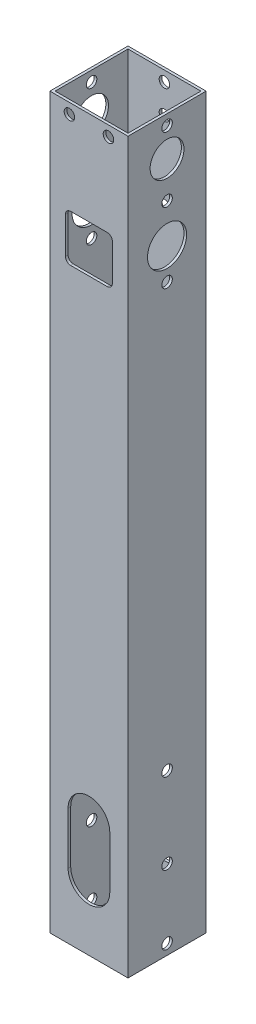
SolidWorks part; units mm, degrees
material "6063-T5"
ref_plane "前视基准面" through (0, 0, 0) normal (0, 0, 1) x (1, 0, 0)
ref_plane "上视基准面" through (0, 0, 0) normal (0, 1, 0) x (1, 0, 0)
ref_plane "右视基准面" through (0, 0, 0) normal (1, 0, 0) x (0, 0, -1)
other "Configuration Table"
sketch "草图1" plane through (0, 0, 0) normal (0, 1, 0) x (1, 0, 0)
  line L1 (-15, -15) -> (15, -15)
  line L2 (-15, -15) -> (-15, 15)
  line L3 (-15, 15) -> (15, 15)
  line L4 (15, -15) -> (15, 15)
  line L5 (-15, -15) -> (15, 15) construction
  line L6 (-15, 15) -> (15, -15) construction
  point P0 (0, 0)
  dimension "D1" = 30
extrude "凸台-拉伸1" add sketch "草图1" along normal mid plane 280
sketch "草图2" plane through (0, 0, 0) normal (0, 1, 0) x (1, 0, 0)
  line L8 (14, -14) -> (14, 14)
  line L9 (14, 14) -> (-14, 14)
  line L10 (-14, 14) -> (-14, -14)
  line L11 (-14, -14) -> (14, -14)
  line L12 (14, -14) -> (14, 14)
  line L13 (14, 14) -> (-14, 14)
  line L14 (-14, 14) -> (-14, -14)
  line L15 (-14, -14) -> (14, -14)
  dimension "D1" = 1
extrude "切除-拉伸1" cut sketch "草图2" against normal through all both and the other way through all
sketch "草图3" plane through (-15, 0, 0) normal (-1, 0, 0) x (0, 0, 1)
  circle A0 centre (0, -78.5) radius 2.025
  circle A1 centre (0, -109.5) radius 2.025
  circle A2 centre (0, -136) radius 2.025
  circle A3 centre (0, -109.5) radius 2.025 construction
  circle A4 centre (0, -78.5) radius 2.025 construction
  circle A5 centre (0, -136) radius 2.025 construction
  dimension "D1" = 4.05
extrude "切除-拉伸2" cut sketch "草图3" against normal through all both
sketch "草图5" plane through (-15, 0, 0) normal (-1, 0, 0) x (0, 0, 1)
  line L0 (15, 140) -> (15, -140) construction
  line L1 (-15, 140) -> (15, 140) construction
  circle A0 centre (0, 136) radius 2.025
  circle A1 centre (0, 111) radius 2.025
  circle A2 centre (0, 84) radius 2.025
  dimension "D1" = 4.05
  dimension "D2" = 15
  dimension "D4" = 25
  dimension "D5" = 27
  dimension "D3" = 4
extrude "切除-拉伸3" cut sketch "草图5" against normal through all
sketch "草图6" plane through (0, 0, -15) normal (0, 0, -1) x (-1, 0, 0)
  line L0 (-15, 140) -> (15, 140) construction
  line L1 (15, 140) -> (15, -140) construction
  circle A0 centre (0, 95) radius 2.025
  circle A1 centre (0, 125) radius 2.025
  dimension "D1" = 4.05
  dimension "D2" = 15
  dimension "D3" = 30
  dimension "D4" = 15
extrude "切除-拉伸4" cut sketch "草图6" against normal up to surface (1 mm away) up to face at (0, 0, -14)
sketch "草图7" plane through (0, 0, 14) normal (0, 0, -1) x (-1, 0, 0)
  line L1 (-9, 86) -> (9, 86)
  line L2 (-9, 86) -> (-9, 104)
  line L3 (-9, 104) -> (9, 104)
  line L4 (9, 86) -> (9, 104)
  line L5 (-9, 86) -> (9, 104) construction
  line L6 (-9, 104) -> (9, 86) construction
  point P0 (0, 95)
  dimension "D1" = 18
  dimension "D2" = 18
extrude "切除-拉伸5" cut sketch "草图7" against normal up to surface (1 mm away) up to face at (0, 0, 15)
fillet "圆角1" radius 2 4 edges at (9, 86, 14.5) (-9, 104, 14.5) (-9, 86, 14.5) (9, 104, 14.5)
sketch "草图8" plane through (0, 0, -15) normal (0, 0, -1) x (-1, 0, 0)
  line L0 (-15, 140) -> (15, 140) construction
  circle A0 centre (0, 136) radius 2.025
  dimension "D1" = 4
  dimension "D2" = 4.05
extrude "切除-拉伸6" cut sketch "草图8" along direction (0, 0, 1) on the side against the normal blind 10
sketch "草图10" plane through (-15, 0, 0) normal (-1, 0, 0) x (0, 0, 1)
  line L2 (-15, 140) -> (15, 140) construction
  circle A1 centre (0, 96) radius 7.5
  circle A2 centre (0, 125) radius 6.5
  dimension "D1" = 15
  dimension "D2" = 13
  dimension "D3" = 15
  dimension "D4" = 44
extrude "切除-拉伸7" cut sketch "草图10" against normal through all both
sketch "草图11" plane through (0, 0, -15) normal (0, 0, -1) x (-1, 0, 0)
  line L0 (0, -115) -> (0, -95) construction
  line L1 (-8, -115) -> (-8, -95)
  line L2 (8, -115) -> (8, -95)
  line L3 (-15, -140) -> (15, -140) construction
  arc A0 (-8, -115) -> (8, -115) centre (0, -115) ccw
  arc A1 (8, -95) -> (-8, -95) centre (0, -95) ccw
  point P3 (0, -105)
  dimension "D1" = 8
  dimension "D2" = 20
  dimension "D3" = 35
extrude "切除-拉伸8" cut sketch "草图11" against normal through all both
sketch "草图12" plane through (0, 0, -14) normal (0, 0, 1) x (1, 0, 0)
  line L0 (-7.5, 136) -> (7.5, 136) construction
  line L1 (-15, 140) -> (15, 140) construction
  line L2 (0, 136) -> (0, 140) construction
  circle A0 centre (-7.5, 136) radius 2.025
  circle A1 centre (7.5, 136) radius 2.025
  dimension "D1" = 4.05
  dimension "D3" = 15
  dimension "D2" = 4
extrude "切除-拉伸9" cut sketch "草图12" against normal blind 10 from surface at 29 starting at face at (0, -105, 15)
